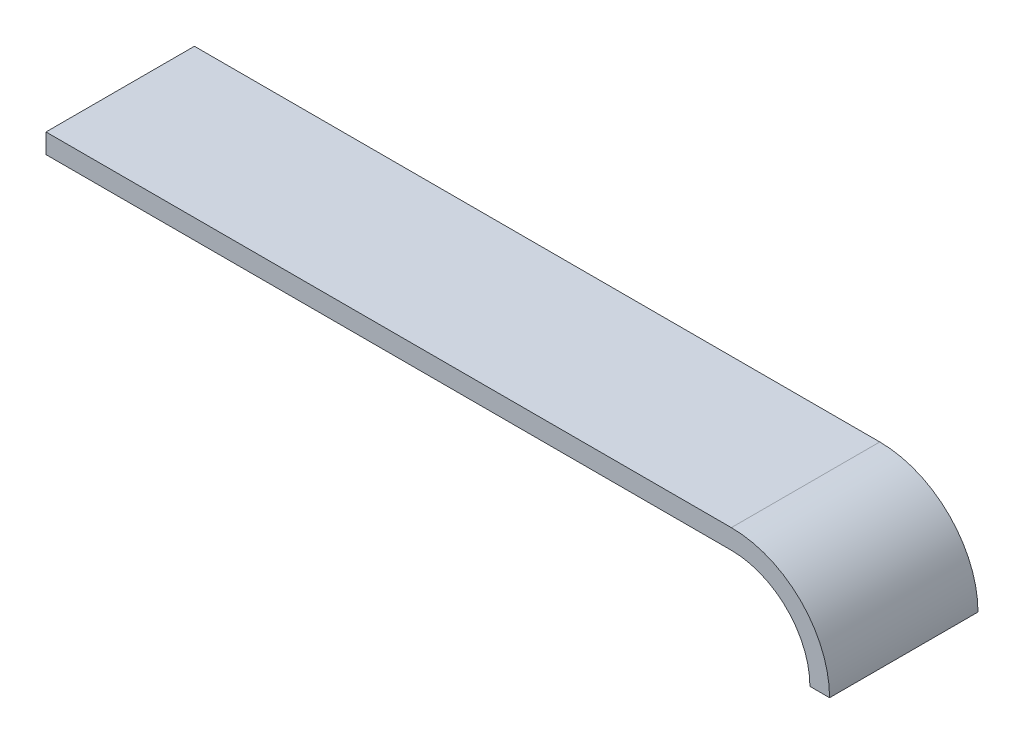
SolidWorks part; units mm, degrees
ref_plane "Front Plane" through (0, 0, 0) normal (0, 0, 1) x (1, 0, 0)
ref_plane "Top Plane" through (0, 0, 0) normal (0, 1, 0) x (1, 0, 0)
ref_plane "Right Plane" through (0, 0, 0) normal (1, 0, 0) x (0, 0, -1)
sketch "Sketch2" plane through (0, 0, 0) normal (0, 0, 1) x (1, 0, 0)
  line L0 (35.6132, -15.9539) -> (37.8632, -15.9539)
  line L1 (-51.8868, -4.7039) -> (26.6132, -4.7039)
  line L2 (-51.8868, -4.7039) -> (-51.8868, -6.9539)
  line L3 (-51.8868, -6.9539) -> (26.6132, -6.9539)
  arc A0 (26.6132, -6.9539) -> (35.6132, -15.9539) centre (26.6132, -15.9539) cw
  arc A1 (26.6132, -4.7039) -> (37.8632, -15.9539) centre (26.6132, -15.9539) cw
extrude "Boss-Extrude1" add sketch "Sketch2" along normal blind 17
